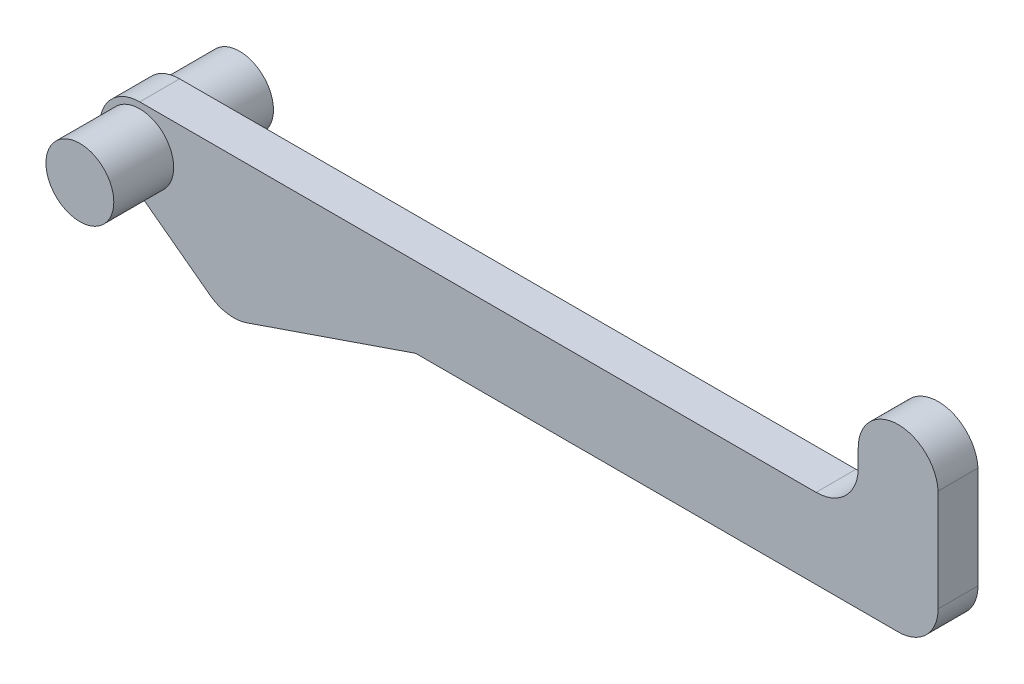
SolidWorks part; units mm, degrees
ref_plane "Plan de face" through (0, 0, 0) normal (0, 0, 1) x (1, 0, 0)
ref_plane "Plan de dessus" through (0, 0, 0) normal (0, 1, 0) x (1, 0, 0)
ref_plane "Plan de droite" through (0, 0, 0) normal (1, 0, 0) x (0, 0, -1)
sketch "Esquisse1" plane through (0, 0, 0) normal (0, 0, 1) x (1, 0, 0)
  line L0 (-38.9997, 10.2265) -> (-81.3374, -4.314)
  line L1 (-90.5667, -2.8704) -> (-108.1152, 10.2265)
  line L5 (-108.1152, 30.2265) -> (61.3139, 30.2265)
  line L6 (71.8848, 40.7974) -> (71.8848, 45.2265)
  line L8 (91.8848, 45.7974) -> (91.8848, 20.2265)
  line L11 (81.8848, 10.2265) -> (-38.9997, 10.2265)
  arc A0 (71.8848, 40.7974) -> (61.3139, 30.2265) centre (61.3139, 40.7974) cw
  arc A1 (91.8848, 20.2265) -> (81.8848, 10.2265) centre (81.8848, 20.2265) cw
  arc A2 (91.8848, 45.7974) -> (71.8848, 45.2265) centre (81.8929, 45.2265) ccw
  arc A3 (-108.1152, 30.2265) -> (-108.1152, 10.2265) centre (-108.1152, 20.2265) ccw
  arc A4 (-81.3374, -4.314) -> (-90.5667, -2.8704) centre (-84.5856, 5.1438) cw
  dimension "D1" = 10
  dimension "D2" = 10
  dimension "D3" = 20
  dimension "D4" = 20
  dimension "D5" = 35
  dimension "D6" = 200
extrude "Boss.-Extru.1" add sketch "Esquisse1" along normal blind 10
sketch "Esquisse2" plane through (0, 0, 10) normal (0, 0, 1) x (1, 0, 0)
  circle A0 centre (-108.1152, 20.2265) radius 8.5
  dimension "D1" = 17
extrude "Boss.-Extru.2" add sketch "Esquisse2" along normal blind 15 and the other way blind 25
